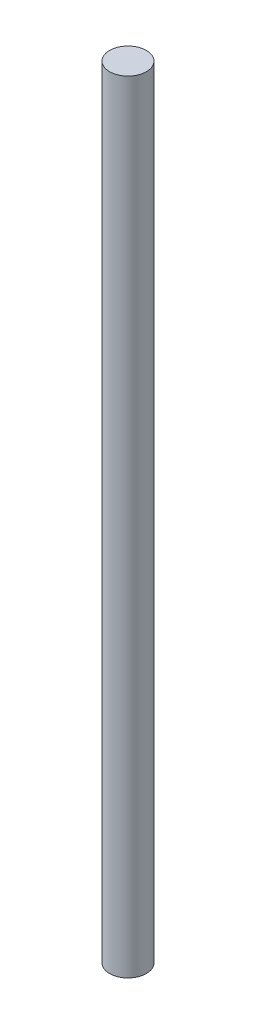
SolidWorks part; units mm, degrees
ref_plane "前视基准面" through (0, 0, 0) normal (0, 0, 1) x (1, 0, 0)
ref_plane "上视基准面" through (0, 0, 0) normal (0, 1, 0) x (1, 0, 0)
ref_plane "右视基准面" through (0, 0, 0) normal (1, 0, 0) x (0, 0, -1)
other "Configuration Table"
sketch "草图1" plane through (0, 0, 0) normal (0, 1, 0) x (1, 0, 0)
  circle A0 centre (0, 0) radius 0.75
  dimension "D1" = 1.5
extrude "凸台-拉伸1" add sketch "草图1" along normal mid plane 31.8
